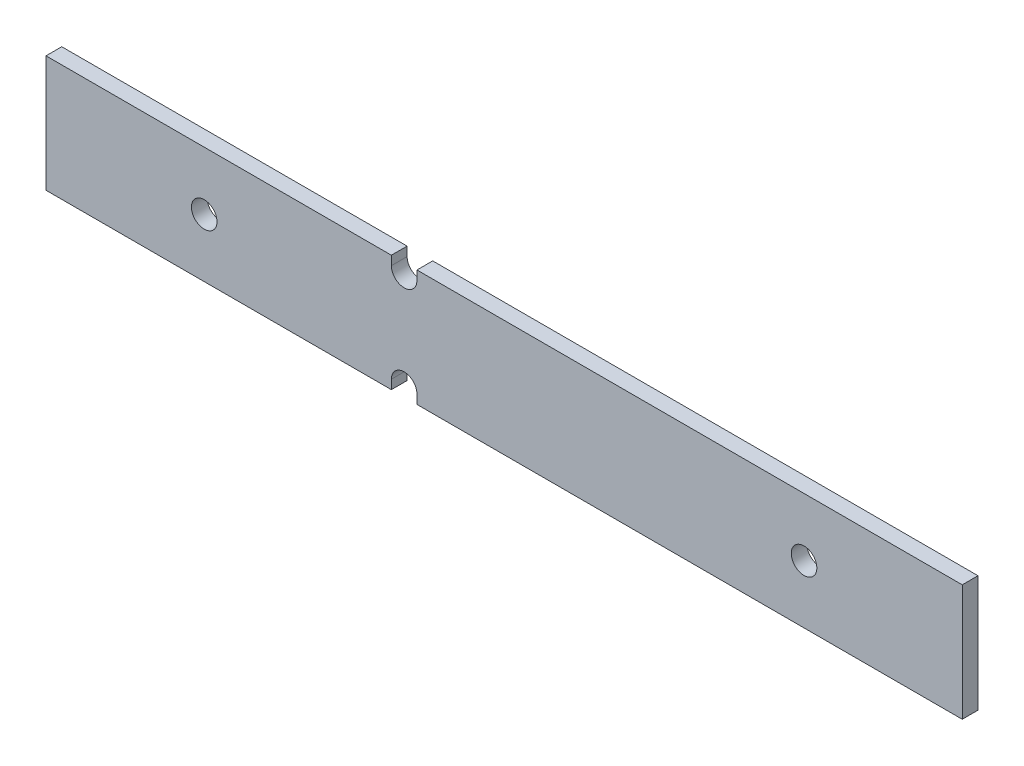
SolidWorks part; units mm, degrees
ref_plane "Front Plane" through (0, 0, 0) normal (0, 0, 1) x (1, 0, 0)
ref_plane "Top Plane" through (0, 0, 0) normal (0, 1, 0) x (1, 0, 0)
ref_plane "Right Plane" through (0, 0, 0) normal (1, 0, 0) x (0, 0, -1)
sketch "Sketch1" plane through (0, 0, 1.63) normal (0, 0, 1) x (1, 0, 0)
  line L1 (5.9182, -5.9182) -> (-87.1982, -5.9182)
  line L2 (5.9182, -5.9182) -> (5.9182, 5.9182)
  line L3 (5.9182, 5.9182) -> (-87.1982, 5.9182)
  line L4 (-87.1982, -5.9182) -> (-87.1982, 5.9182)
  line L5 (5.9182, -5.9182) -> (-87.1982, 5.9182) construction
  line L6 (5.9182, 5.9182) -> (-87.1982, -5.9182) construction
  line L7 (-4.3624, -5.9182) -> (4.3624, -5.9182) construction
  line L8 (5.9182, -4.3625) -> (5.9182, 4.3625) construction
  line L9 (4.3624, 5.9182) -> (-4.3624, 5.9182) construction
  line L10 (-87.1982, 4.3624) -> (-87.1982, -4.3624) construction
  point P4 (-40.64, 0)
extrude "Boss-Extrude1" add sketch "Sketch1" along normal blind 1.6002
hole_wizard "Ø2.6 (2.6) Diameter Hole1" positions "Sketch3" profile "Sketch2" hole size "Ø2.6" standard "ANSI Metric" end condition through all
sketch "Sketch3" plane through (0, 0, 3.2302) normal (0, 0, 1) x (1, 0, 0)
  line L0 (-87.1982, 0) -> (5.9182, 0) construction
  line L3 (-87.1982, 5.9182) -> (-87.1982, -5.9182) construction
  line L7 (5.9182, -5.9182) -> (5.9182, 5.9182) construction
  point P0 (-50.8, 4.9975)
  point P23 (-50.8, -4.9975)
  point P32 (-10.16, 0)
  point P35 (-71.12, 0)
sketch "Sketch2" plane through (-50.8, 4.9975, 3.2302) normal (1, 0, 0) x (0, -1, 0)
  line L0 (0, 0) -> (0, 1.6002)
  line L1 (0, 1.6002) -> (1.3, 1.6002)
  line L2 (1.3, 1.6002) -> (1.3, 0)
  line L5 (1.3, 0) -> (0, 0)
  line L11 (0, -6.35) -> (0, 107.95) construction
  dimension "Thru Hole Dia." = 2.6
  dimension "Thru Hole Depth" = 1.6002
sketch "Sketch6" plane through (0, 0, 3.2302) normal (0, 0, 1) x (1, 0, 0)
  line L0 (5.9182, 5.9182) -> (-49.8823, 5.9182) construction
  line L1 (-52.1, 4.9975) -> (-49.5, 4.9975)
  line L2 (-52.1, 4.9975) -> (-52.1, 5.9182)
  line L3 (-52.1, 5.9182) -> (-49.5, 5.9182)
  line L4 (-49.5, 4.9975) -> (-49.5, 5.9182)
  line L5 (-49.8823, -5.9182) -> (5.9182, -5.9182) construction
  line L6 (-52.1, -4.9975) -> (-49.5, -4.9975)
  line L7 (-52.1, -4.9975) -> (-52.1, -5.9182)
  line L8 (-52.1, -5.9182) -> (-49.5, -5.9182)
  line L9 (-49.5, -4.9975) -> (-49.5, -5.9182)
  arc A0 (-51.7177, 5.9182) -> (-49.8823, 5.9182) centre (-50.8, 4.9975) ccw construction
  arc A1 (-49.8823, -5.9182) -> (-51.7177, -5.9182) centre (-50.8, -4.9975) ccw construction
extrude "Cut-Extrude1" cut sketch "Sketch6" against normal through all
sketch "REAR COMPONENT KEEP OUT ZONE" plane through (0, 0, 3.2302) normal (0, 0, 1) x (1, 0, 0)
  line L0 (-53.74, -4.9975) -> (-53.74, -8.6836) construction
  line L1 (-47.8599, -8.6836) -> (-47.8599, -4.9975) construction
  line L2 (-53.74, -4.9975) -> (-53.74, -5.9182)
  line L3 (-47.8599, -5.9182) -> (-47.8599, -4.9975)
  line L7 (-47.8599, 5.9182) -> (-47.8599, 4.9975)
  line L8 (-53.74, 4.9975) -> (-53.74, 5.946)
  line L9 (-53.74, -5.9182) -> (-47.8599, -5.9182)
  line L10 (-87.1982, -5.9182) -> (-52.1, -5.9182) construction
  line L11 (-49.5, -5.9182) -> (5.9182, -5.9182) construction
  line L12 (-53.74, 5.946) -> (-47.8599, 5.9182)
  line L13 (5.9182, 5.9182) -> (-49.5, 5.9182) construction
  arc A0 (-47.8599, -4.9975) -> (-53.74, -4.9975) centre (-50.8, -4.9975) ccw construction
  arc A1 (-47.8599, -4.9975) -> (-53.74, -4.9975) centre (-50.8, -4.9975) ccw
  circle A2 centre (-33.73, 0) radius 2.3813 construction
  circle A3 centre (-71.12, 0) radius 2.3813 construction
  circle A4 centre (-10.16, 0) radius 2.3813 construction
  circle A5 centre (-33.73, 0) radius 2.3812
  circle A6 centre (-71.12, 0) radius 2.3813
  circle A7 centre (-10.16, 0) radius 2.3813
  circle A8 centre (-30.48, 0) radius 2.3812 construction
  circle A9 centre (-50.8, 0) radius 2.3812 construction
  circle A10 centre (-30.48, 0) radius 2.3812
  circle A11 centre (-50.8, 0) radius 2.3812
  arc A12 (-47.8599, 4.9975) -> (-53.74, 4.9975) centre (-50.8, 4.9975) cw
sketch "FRONT COMPONENT KEEP OUT ZONE" plane through (0, 0, 1.63) normal (0, 0, -1) x (-1, 0, 0)
  line L0 (53.74, -4.9975) -> (53.74, -5.9182) construction
  line L1 (47.8599, -5.9182) -> (47.8599, -4.9975) construction
  line L2 (53.74, -4.9975) -> (53.74, -5.9182)
  line L3 (47.8599, -5.9182) -> (47.8599, -4.9975)
  line L5 (53.74, 5.946) -> (47.8599, 5.9182)
  line L8 (47.8599, 5.9182) -> (47.8599, 4.9975)
  line L9 (53.74, 4.9975) -> (53.74, 5.946)
  circle A0 centre (10.16, 0) radius 2.3813 construction
  circle A1 centre (71.12, 0) radius 2.3813 construction
  arc A2 (53.74, -4.9975) -> (47.8599, -4.9975) centre (50.8, -4.9975) ccw construction
  circle A3 centre (10.16, 0) radius 2.3813
  circle A4 centre (71.12, 0) radius 2.3813
  arc A5 (53.74, -4.9975) -> (47.8599, -4.9975) centre (50.8, -4.9975) ccw
  arc A6 (53.74, 4.9975) -> (47.8599, 4.9975) centre (50.8, 4.9975) cw
